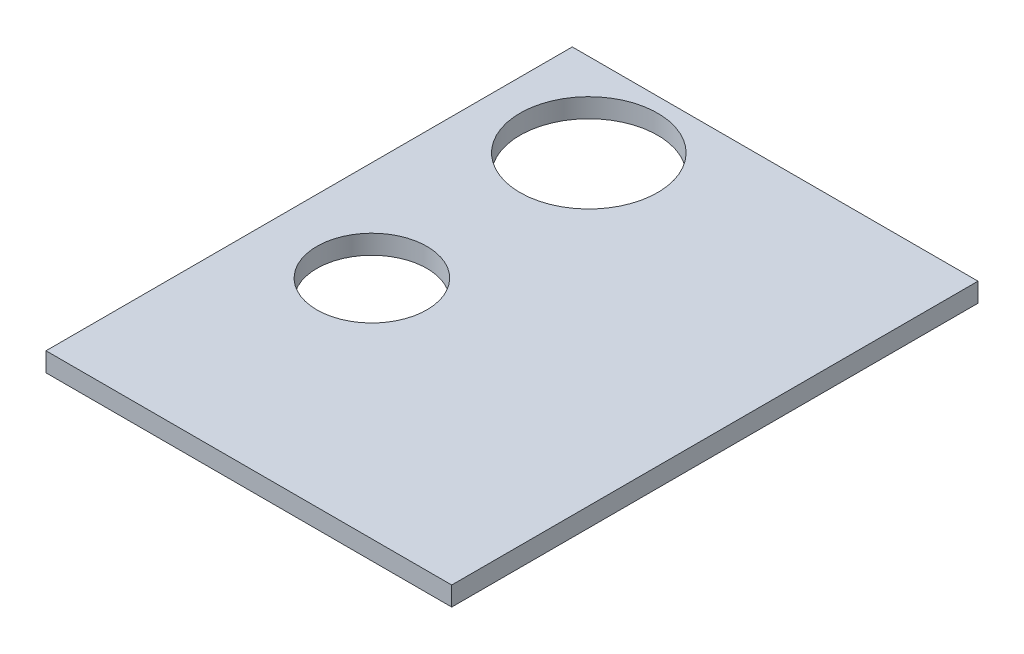
SolidWorks part; units mm, degrees
ref_plane "Plan de face" through (0, 0, 0) normal (0, 0, 1) x (1, 0, 0)
ref_plane "Plan de dessus" through (0, 0, 0) normal (0, 1, 0) x (1, 0, 0)
ref_plane "Plan de droite" through (0, 0, 0) normal (1, 0, 0) x (0, 0, -1)
sketch "Esquisse1" plane through (0, 0, 0) normal (0, 1, 0) x (1, 0, 0)
  line L1 (0, 0) -> (84.8032, 0)
  line L2 (0, 0) -> (0, -110)
  line L3 (0, -110) -> (84.8032, -110)
  line L4 (84.8032, 0) -> (84.8032, -110)
  dimension "D1" = 110
extrude "Boss.-Extru.1" add sketch "Esquisse1" along normal blind 4
sketch "Esquisse2" plane through (0, 4, 0) normal (0, 1, 0) x (1, 0, 0)
  line L0 (20.9047, -17.4483) -> (20.9047, -62.7908) construction
  circle A0 centre (20.9047, -17.4483) radius 14.3832
  circle A1 centre (20.9047, -62.7908) radius 11.5
  dimension "D1" = 23
extrude "Enlèv. mat.-Extru.1" cut sketch "Esquisse2" against normal through all
